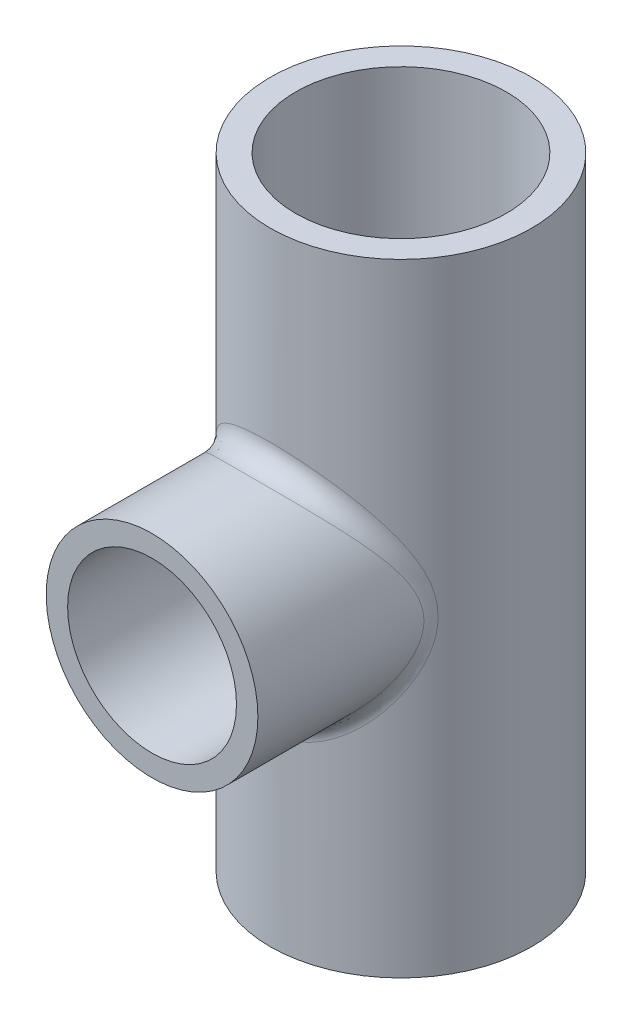
SolidWorks part; units mm, degrees
ref_plane "Front Plane" through (0, 0, 0) normal (0, 0, 1) x (1, 0, 0)
ref_plane "Top Plane" through (0, 0, 0) normal (0, 1, 0) x (1, 0, 0)
ref_plane "Right Plane" through (0, 0, 0) normal (1, 0, 0) x (0, 0, -1)
sketch "Sketch2" plane through (0, 0, 0) normal (0, 1, 0) x (1, 0, 0)
  circle A0 centre (0, 0) radius 0.6565
  dimension "D1" = 1.313
extrude "Boss-Extrude1" add sketch "Sketch2" along normal blind 3.125
sketch "Sketch3" plane through (0, 0, 0) normal (0, 0, 1) x (1, 0, 0)
  circle A0 centre (0, 1.5625) radius 0.5315
  dimension "D1" = 1.063
extrude "Boss-Extrude2" add sketch "Sketch3" along normal blind 1.25
fillet "Fillet1" radius 0.1 1 edges at (0.5245, 1.6487, 0.3949)
sketch "Sketch4" plane through (0, 3.125, 0) normal (0, 1, 0) x (1, 0, 0)
  circle A0 centre (0, 0) radius 0.529
  dimension "D1" = 1.058
extrude "Cut-Extrude1" cut sketch "Sketch4" against normal blind 1.25
sketch "Sketch5" plane through (0, 0, 0) normal (0, -1, 0) x (1, 0, 0)
  circle A0 centre (0, 0) radius 0.529
  dimension "D1" = 1.058
extrude "Cut-Extrude2" cut sketch "Sketch5" against normal blind 1.25
sketch "Sketch6" plane through (0, 1.875, 0) normal (0, 1, 0) x (1, 0, 0)
  circle A0 centre (0, 0) radius 0.412
  dimension "D1" = 0.824
extrude "Cut-Extrude3" cut sketch "Sketch6" against normal through all
sketch "Sketch7" plane through (0, 0, 1.25) normal (0, 0, 1) x (1, 0, 0)
  circle A0 centre (0, 1.5625) radius 0.311
  dimension "D1" = 0.622
extrude "Cut-Extrude4" cut sketch "Sketch7" against normal blind 1.25
sketch "Sketch8" plane through (0, 0, 1.25) normal (0, 0, 1) x (1, 0, 0)
  circle A0 centre (0, 1.5625) radius 0.424
  dimension "D1" = 0.848
extrude "Cut-Extrude5" cut sketch "Sketch8" against normal blind 0.69
